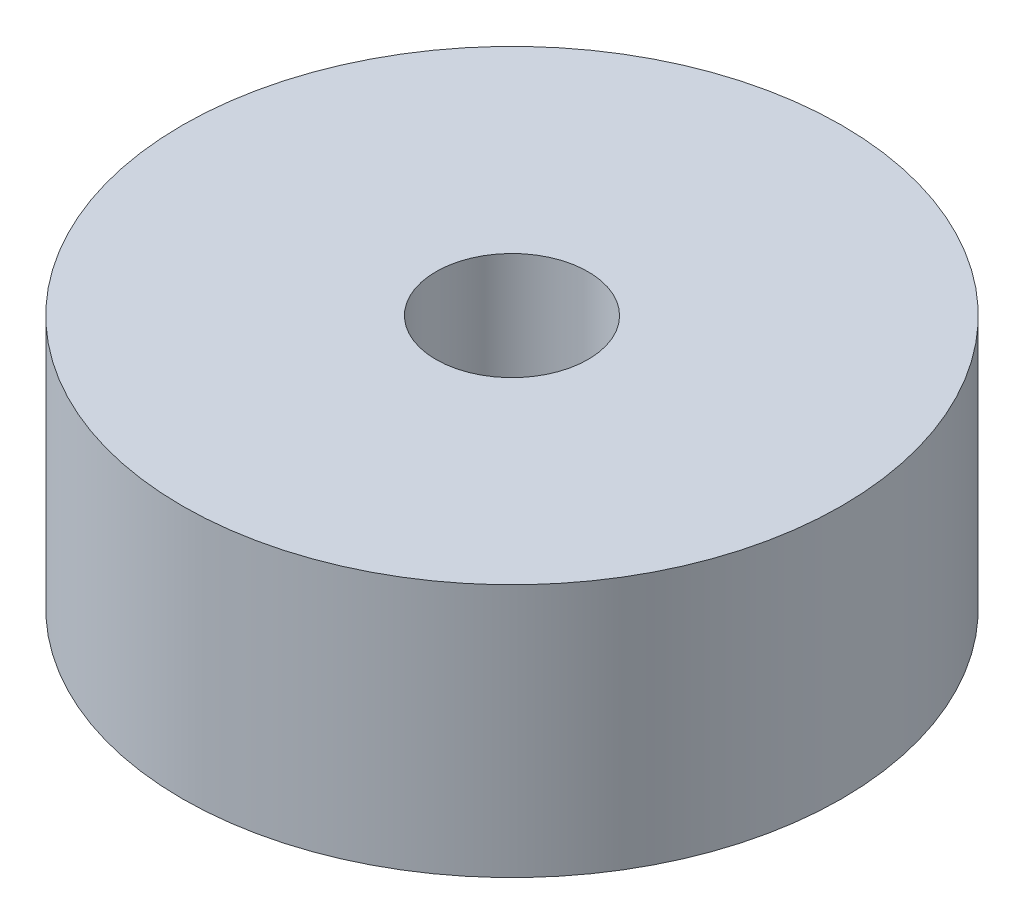
SolidWorks part; units mm, degrees
ref_plane "Front Plane" through (0, 0, 0) normal (0, 0, 1) x (1, 0, 0)
ref_plane "Top Plane" through (0, 0, 0) normal (0, 1, 0) x (1, 0, 0)
ref_plane "Right Plane" through (0, 0, 0) normal (1, 0, 0) x (0, 0, -1)
sketch "Sketch1" plane through (0, 0, 0) normal (0, 1, 0) x (1, 0, 0)
  circle A0 centre (0, 0) radius 1.5
  circle A1 centre (0, 0) radius 6.5
  dimension "D1" = 3
  dimension "D2" = 13
extrude "Boss-Extrude1" add sketch "Sketch1" along normal blind 5
